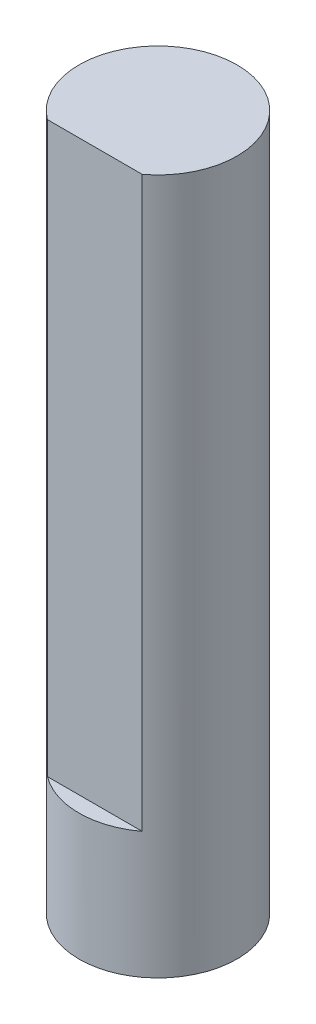
SolidWorks part; units mm, degrees
ref_plane "前视基准面" through (0, 0, 0) normal (0, 0, 1) x (1, 0, 0)
ref_plane "上视基准面" through (0, 0, 0) normal (0, 1, 0) x (1, 0, 0)
ref_plane "右视基准面" through (0, 0, 0) normal (1, 0, 0) x (0, 0, -1)
sketch "草图1" plane through (0, 0, 0) normal (0, 1, 0) x (1, 0, 0)
  circle A0 centre (0, 0) radius 2.5
  dimension "D1" = 5
extrude "凸台-拉伸1" add sketch "草图1" along normal blind 22
ref_plane "基准面1" through (0, 0, 2.5) normal (0, 0, 1) x (1, 0, 0)
sketch "草图2" plane through (0, 0, 2.5) normal (0, 0, 1) x (1, 0, 0)
  line L0 (2.5, 0) -> (2.5, 22) construction
  line L1 (-2.5, 22) -> (2.5, 22)
  line L2 (-2.5, 22) -> (-2.5, 4)
  line L3 (-2.5, 4) -> (2.5, 4)
  line L4 (2.5, 22) -> (2.5, 4)
  dimension "D1" = 18
extrude "切除-拉伸1" cut sketch "草图2" against normal blind 0.5
